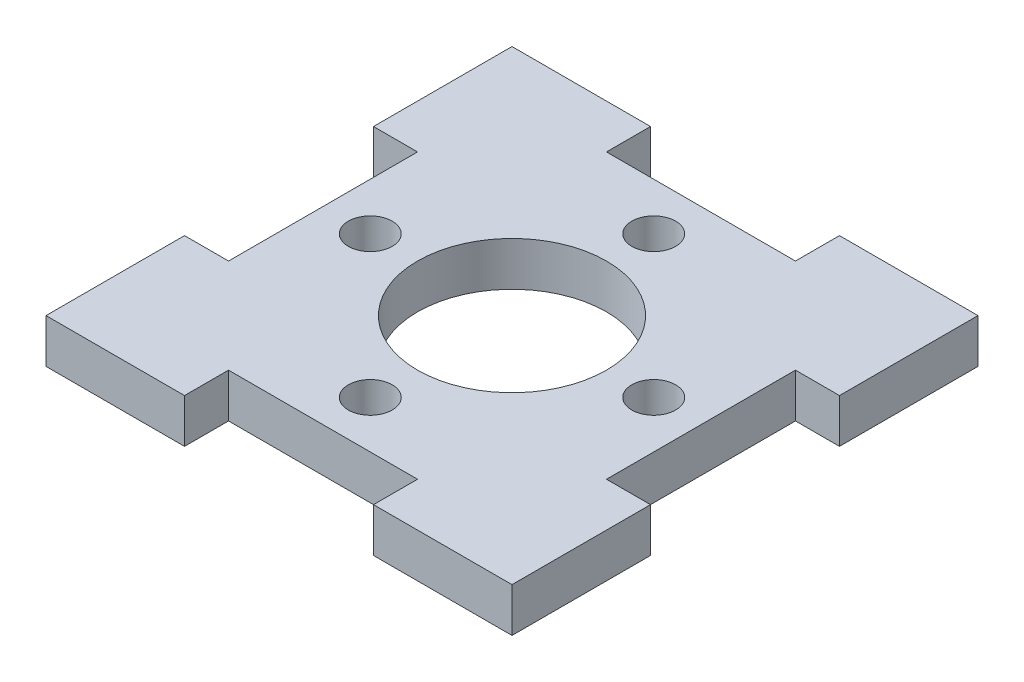
SolidWorks part; units mm, degrees
ref_plane "Front Plane" through (0, 0, 0) normal (0, 0, 1) x (1, 0, 0)
ref_plane "Top Plane" through (0, 0, 0) normal (0, 1, 0) x (1, 0, 0)
ref_plane "Right Plane" through (0, 0, 0) normal (1, 0, 0) x (0, 0, -1)
sketch "Sketch1" plane through (0, 0, 0) normal (0, 1, 0) x (1, 0, 0)
  line L0 (6.35, 15.6591) -> (15.6591, 15.6591)
  line L1 (-15.6591, 15.6591) -> (-6.35, 15.6591)
  line L2 (-15.6591, 15.6591) -> (-15.6591, 6.35)
  line L3 (-15.6591, -15.6591) -> (-6.35, -15.6591)
  line L4 (15.6591, 15.6591) -> (15.6591, 6.35)
  line L5 (-15.6591, 15.6591) -> (15.6591, -15.6591) construction
  line L6 (-15.6591, -15.6591) -> (15.6591, 15.6591) construction
  line L7 (15.6591, 6.35) -> (12.7, 6.35)
  line L8 (-6.35, 15.6591) -> (-6.35, 12.7)
  line L9 (-6.35, 12.7) -> (6.35, 12.7)
  line L10 (6.35, 15.6591) -> (6.35, 12.7)
  line L11 (12.7, 6.35) -> (12.7, -6.35)
  line L12 (15.6591, -6.35) -> (12.7, -6.35)
  line L13 (6.35, -15.6591) -> (6.35, -12.7)
  line L14 (6.35, -12.7) -> (-6.35, -12.7)
  line L15 (-6.35, -15.6591) -> (-6.35, -12.7)
  line L16 (-15.6591, -6.35) -> (-12.7, -6.35)
  line L17 (-12.7, -6.35) -> (-12.7, 6.35)
  line L18 (-15.6591, 6.35) -> (-12.7, 6.35)
  line L19 (15.6591, -6.35) -> (15.6591, -15.6591)
  line L20 (6.35, -15.6591) -> (15.6591, -15.6591)
  line L21 (-15.6591, -6.35) -> (-15.6591, -15.6591)
  circle A0 centre (0, 9.525) radius 1.4732 construction
  circle A1 centre (9.525, 0) radius 1.4732 construction
  circle A2 centre (0, -9.525) radius 1.4732 construction
  circle A3 centre (-9.525, 0) radius 1.4732 construction
  circle A4 centre (0, 0) radius 9.525 construction
  circle A5 centre (0, 0) radius 6.35
  point P0 (0, 0)
  point P17 (0, 0)
  point P22 (0, 12.7)
  point P38 (0, 0)
  dimension "D4" = 2.9464
  dimension "D6" = 12.7
  dimension "D1" = 25.4
  dimension "D3" = 9.525
  dimension "D7" = 12.7
  dimension "D8" = 2.9591
  dimension "D5" = 4
  dimension "D9" = 4
extrude "Boss-Extrude1" add sketch "Sketch1" along normal blind 2.9591 contours L4 L1 L2 L3 A5
hole_wizard "#4 Clearance Hole1" positions "Sketch3" profile "Sketch4" hole size "#4" standard "ANSI Inch" end condition up to next
sketch "Sketch3" plane through (-7.7973, 2.9591, -11.4721) normal (0, 1, 0) x (1, 0, 0)
  point P0 (7.7973, -1.9471)
  point P3 (17.3223, -11.4721)
  point P6 (7.7973, -20.9971)
  point P9 (-1.7277, -11.4721)
sketch "Sketch4" plane through (0, 2.9591, -9.525) normal (1, 0, 0) x (0, 0, 1)
  line L0 (0, 0) -> (0, 2.9591)
  line L1 (0, 2.9591) -> (1.4732, 2.9591)
  line L2 (1.4732, 2.9591) -> (1.4732, 0)
  line L5 (1.4732, 0) -> (0, 0)
  line L11 (0, -6.35) -> (0, 107.95) construction
  dimension "Thru Hole Dia." = 2.9464
  dimension "Thru Hole Depth" = 2.9591
